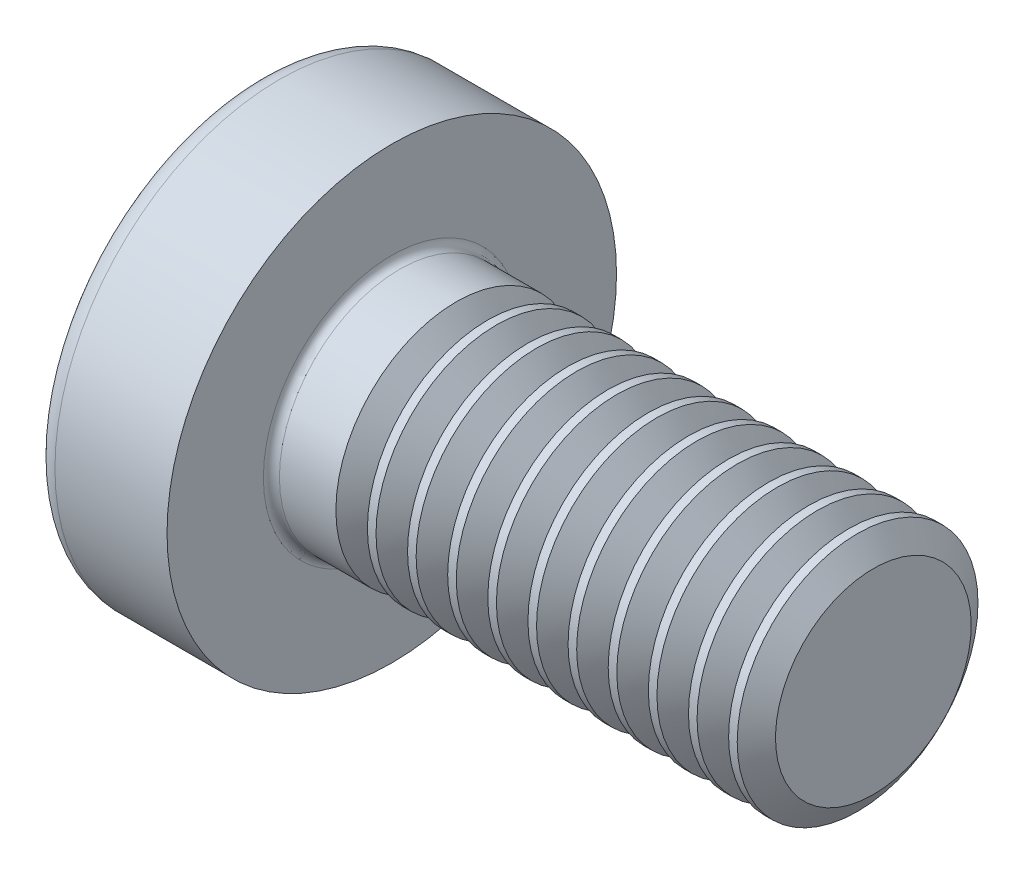
SolidWorks part; units mm, degrees
ref_plane "Plane1" through (0, 0, 0) normal (0, 0, 1) x (1, 0, 0)
ref_plane "Plane2" through (0, 0, 0) normal (0, 1, 0) x (1, 0, 0)
ref_plane "Plane3" through (0, 0, 0) normal (1, 0, 0) x (0, 0, -1)
sketch "BodySke" plane through (0, 0, 0) normal (0, 0, 1) x (1, 0, 0)
  line L0 (2.4, 1.5) -> (2.4, 2.8)
  line L1 (2.65, 6.35) -> (2.65, -3.175) construction
  line L2 (-25.4, 0) -> (127, 0) construction
  line L3 (8.4, 0) -> (0, 0)
  line L4 (2.4, 1.5) -> (8.4, 1.5)
  line L5 (8.4, 1.5) -> (8.4, 0)
  line L6 (1.0035, 2.8) -> (2.4, 2.8)
  line L8 (2.4, 6.35) -> (2.4, -3.175) construction
  arc A0 (0.7754, 2.6744) -> (0, 0) centre (5, 0) ccw
  arc A2 (0.7754, 2.6744) -> (1.0035, 2.8) centre (1.0035, 2.53) cw
revolve "Base-Revolve" add sketch "BodySke"
cosmetic thread "ThreadCosmetic" [suppressed]
fillet "Fillet1" radius 0.1 1 edges at (2.4, 0, 1.5)
sketch "Sketch3" plane through (0, 0, 0) normal (1, 0, 0) x (0, 0, -1)
  line L0 (0.37, -1.4) -> (-0.37, -1.4)
  line L1 (0.37, -1.4) -> (0.37, 1.4)
  line L2 (-0.37, 1.4) -> (0.37, 1.4)
  line L3 (-0.37, 1.4) -> (-0.37, -1.4)
ref_plane "Plane4" through (1.75, 0, 0) normal (1, 0, 0) x (0, 0, -1)
sketch "Sketch4" plane through (1.75, 0, 0) normal (1, 0, 0) x (0, 0, -1)
  line L0 (0.37, -0.5275) -> (-0.37, -0.5275)
  line L1 (0.37, -0.5275) -> (0.37, 0.5275)
  line L2 (-0.37, 0.5275) -> (0.37, 0.5275)
  line L3 (-0.37, 0.5275) -> (-0.37, -0.5275)
loft "Recess" cut profiles "Sketch3", "Sketch4"
pattern_circular "RecPat" count 2 every 90 about axis through (0, 0, 0) along (1, 0, 0) of "Recess"
sketch "RecCorSke" plane through (0, 0, 0) normal (0, 0, 1) x (1, 0, 0)
  line L0 (-3.175, 0) -> (15.875, 0) construction
  line L1 (-25.4, 0) -> (127, 0) construction
  line L2 (0, 0) -> (0, 0.6784)
  line L3 (0, 0.6784) -> (1.75, 0.556)
  line L4 (1.75, 0.556) -> (1.9307, 0)
  line L5 (1.9307, 0) -> (0, 0)
revolve "RecessCore" cut sketch "RecCorSke" angle 360 about L0
sketch "ThdSchSke" plane through (0, 0, 0) normal (0, 0, 1) x (1, 0, 0)
  line L0 (3.4, -1.2195) -> (3.2036, -1.5)
  line L1 (3.4, -1.2195) -> (3.5964, -1.5)
  line L2 (3.5964, -1.5) -> (3.5964, -1.875)
  line L3 (-3.175, 0) -> (5.1513, 0) construction
  line L5 (3.5964, -1.875) -> (3.2036, -1.875)
  line L6 (3.2036, -1.875) -> (3.2036, -1.5)
revolve "ThreadSchematic" cut sketch "ThdSchSke" angle 360 about L3
pattern_linear "ThdSchPat" count 11 spacing 0.5 along (1, 0, 0) of "ThreadSchematic"
equation "\"D1@Sketch3\" = \"Cross_dia@Sketch3\" / 2"
equation "\"D2@Sketch3\" = \"Cross_width@Sketch3\" / 2"
equation "\"Depth@RecCorSke\" = \"Cross_depth@Plane4\""
equation "\"D1@Sketch4\" = \"Cross_width@Sketch3\""
equation "\"D2@Sketch4\" = \"Cross_dia@Sketch3\" - 2.0 * \"Cross_depth@Plane4\" * tan(26.5  * 0.017453292)"
equation "\"D3@Sketch4\" = \"D1@Sketch4\" / 2"
equation "\"D4@Sketch4\" = \"D2@Sketch4\" / 2"
equation "\"Thread_length@ThreadCosmetic\" = ((sgn( (\"Length@BodySke\" - \"Advance@BodySke\" * 2.0 ) - \"Thread_nom@BodySke\" )-1)*( (\"Length@BodySke\" - \"Advance@BodySke\" * 2.0 ) - \"Thread_nom@BodySke\" ))/-2+ \"Thread_nom@BodySke\""
equation "\"Thread_minor@ThdSchSke\" = \"Thread_minor@ThreadCosmetic\""
equation "\"Diameter@ThdSchSke\" = \"Diameter@BodySke\""
equation "\"Overcut@ThdSchSke\" = \"Diameter@BodySke\" * 1.25"
equation "\"Start@ThdSchSke\" = \"Head_ht@BodySke\" + \"Length@BodySke\" - \"Thread_length@ThreadCosmetic\"  '---Non-countersunk---"
equation "\"Num_threads@ThdSchPat\" = int( \"Thread_length@ThreadCosmetic\" / \"Advance@BodySke\" + 0.999 )  + 1"
equation "\"Advance@ThdSchPat\" = \"Thread_length@ThreadCosmetic\" /  (\"Num_threads@ThdSchPat\" - 1) 'relax it"
